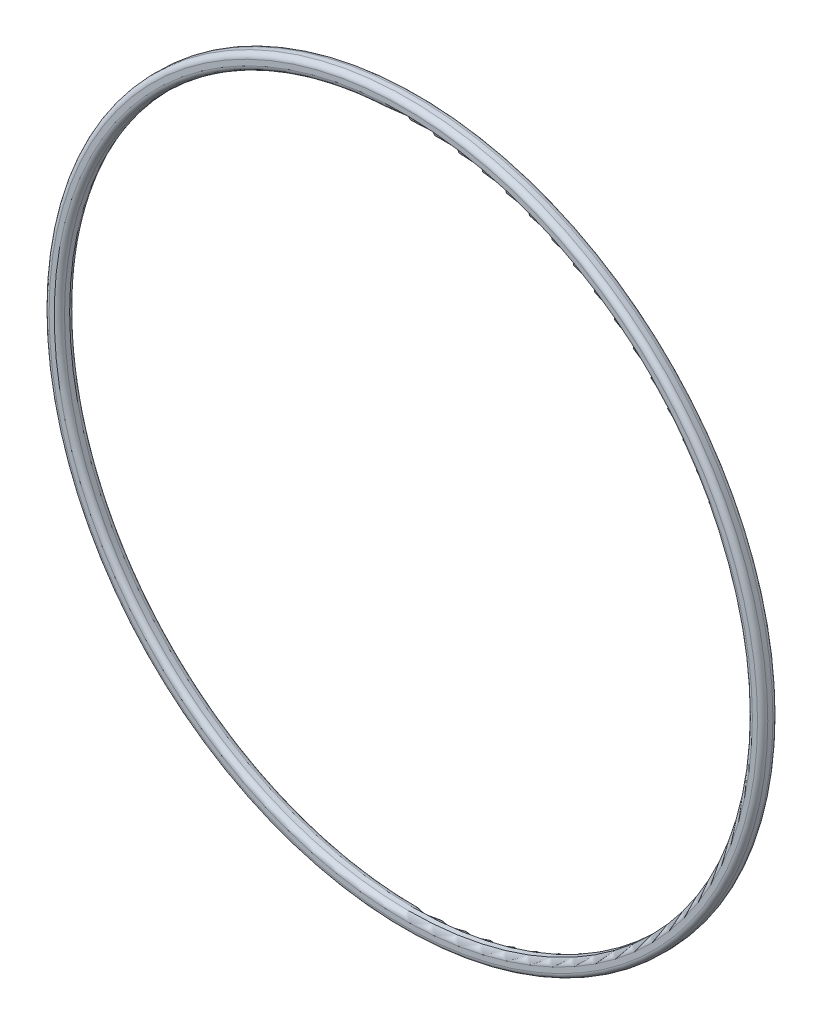
SolidWorks part; units mm, degrees
material "Gomma siliconata"
ref_plane "Piano frontale" through (0, 0, 0) normal (0, 0, 1) x (1, 0, 0)
ref_plane "Piano superiore" through (0, 0, 0) normal (0, 1, 0) x (1, 0, 0)
ref_plane "Piano destro" through (0, 0, 0) normal (1, 0, 0) x (0, 0, -1)
sketch "Schizzo1" plane through (0, 0, 0) normal (0, 0, 1) x (1, 0, 0)
  circle A0 centre (0, 0) radius 67
  circle A1 centre (0, 0) radius 70
  dimension "D1" = 134
  dimension "D2" = 140
extrude "Estrusione-Estrusione1" add sketch "Schizzo1" along normal blind 3
fillet "Raccordo1" radius 1 4 edges at (67, 0, 0) (70, 0, 0) (67, 0, 3) (70, 0, 3)
